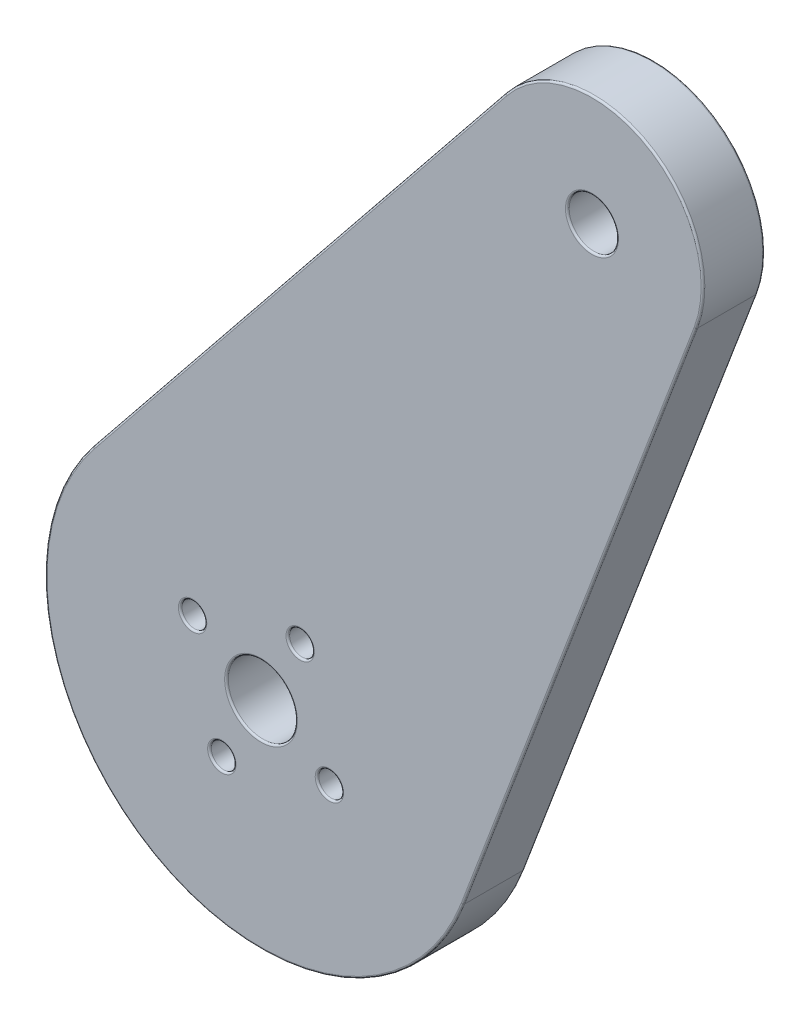
SolidWorks part; units mm, degrees
ref_plane "Front Plane" through (0, 0, 0) normal (0, 0, 1) x (1, 0, 0)
ref_plane "Top Plane" through (0, 0, 0) normal (0, 1, 0) x (1, 0, 0)
ref_plane "Right Plane" through (0, 0, 0) normal (1, 0, 0) x (0, 0, -1)
sketch "Sketch1" plane through (0, 0, 0) normal (0, 0, 1) x (1, 0, 0)
  line L0 (-20.22, 57.58) -> (6.6128, 104.4415) construction
  line L1 (-20.22, 57.58) -> (6.6128, 104.4415) construction
  line L2 (-33.8485, 68.5579) -> (-0.3961, 110.0873)
  line L3 (-3.8539, 51.3831) -> (15.0296, 101.2545)
  line L4 (-20.22, 57.58) -> (-35.4066, 66.2758) construction
  circle A0 centre (-20.22, 57.58) radius 17.5 construction
  circle A1 centre (-20.22, 57.58) radius 17.5 construction
  circle A2 centre (6.6128, 104.4415) radius 9 construction
  arc A3 (-3.8539, 51.3831) -> (-33.8485, 68.5579) centre (-20.22, 57.58) cw
  arc A4 (-0.3961, 110.0873) -> (15.0296, 101.2545) centre (6.6128, 104.4415) cw
  circle A5 centre (-20.22, 57.58) radius 2.8
  circle A6 centre (6.6128, 104.4415) radius 2
  circle A7 centre (-25.7653, 60.7552) radius 1
  circle A8 centre (-17.0448, 63.1253) radius 1
  circle A9 centre (-23.3952, 52.0347) radius 1
  circle A10 centre (-14.6747, 54.4048) radius 1
  dimension "D1" = 18
  dimension "D2" = 4
  dimension "D3" = 5.6
  dimension "D4" = 6.39
  dimension "D5" = 2
  dimension "D6" = 2
  dimension "D7" = 6.39
extrude "Boss-Extrude1" add sketch "Sketch1" against normal blind 5
fillet "Fillet1" radius 0.15 20 edges at (5.5878, 76.3188, -5) (11.0849, 112.2518, -5) (-17.1223, 89.3226, -5) (-28.9158, 42.3934, -5) (-17.42, 57.58, -5) (8.6128, 104.4415, -5) (-17.1223, 89.3226, 0) (11.0849, 112.2518, 0) (5.5878, 76.3188, 0) (-28.9158, 42.3934, 0) (-17.42, 57.58, 0) (8.6128, 104.4415, 0) (-24.7653, 60.7552, -5) (-16.0448, 63.1253, -5) (-24.3952, 52.0347, -5) (-15.6747, 54.4048, -5) (-24.7653, 60.7552, 0) (-16.0448, 63.1253, 0) (-24.3952, 52.0347, 0) (-15.6747, 54.4048, 0)
